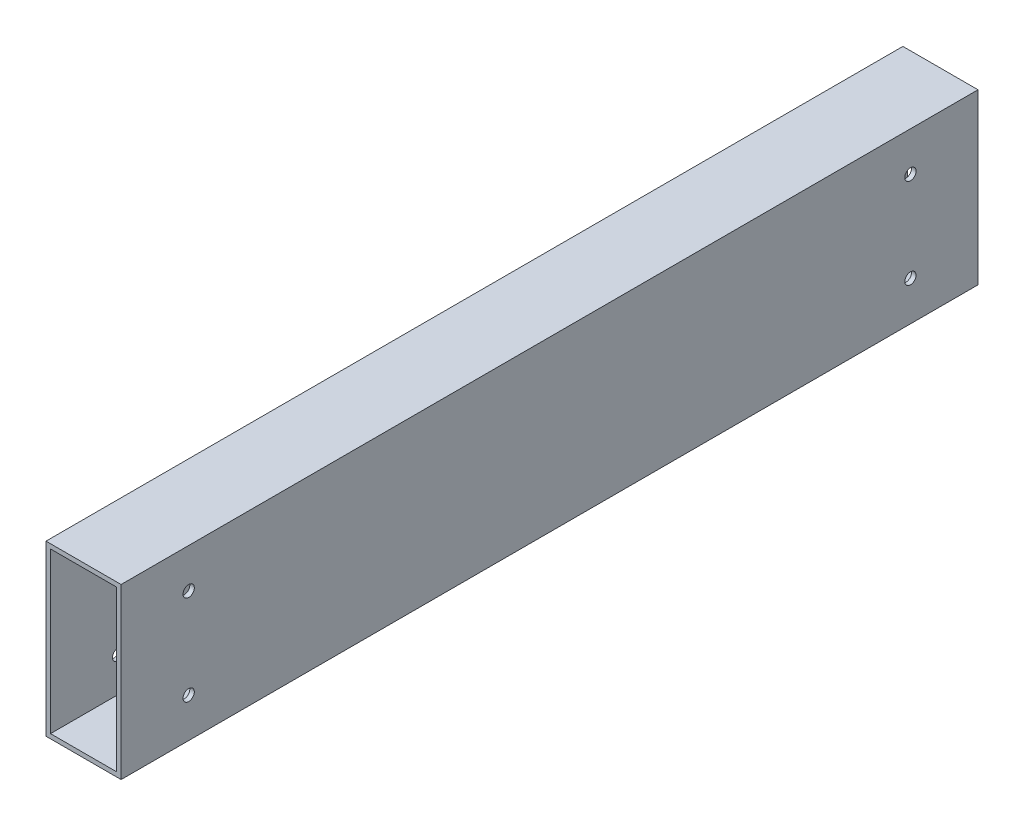
SolidWorks part; units mm, degrees
ref_plane "Alzado" through (0, 0, 0) normal (0, 0, 1) x (1, 0, 0)
ref_plane "Planta" through (0, 0, 0) normal (0, 1, 0) x (1, 0, 0)
ref_plane "Vista lateral" through (0, 0, 0) normal (1, 0, 0) x (0, 0, -1)
sketch "Croquis1" plane through (0, 0, 0) normal (0, 0, 1) x (1, 0, 0)
  line L1 (-10, -22.5) -> (10, -22.5)
  line L2 (-10, -22.5) -> (-10, 22.5)
  line L3 (-10, 22.5) -> (10, 22.5)
  line L4 (10, -22.5) -> (10, 22.5)
  line L5 (-10, -22.5) -> (10, 22.5) construction
  line L6 (-10, 22.5) -> (10, -22.5) construction
  point P0 (0, 0)
extrude "Saliente-Extruir1" add sketch "Croquis1" along normal blind 228.2
sketch "Croquis5" plane through (0, 0, 0) normal (0, 0, -1) x (-1, 0, 0)
  line L0 (-10, 22.5) -> (10, 22.5) construction
  line L1 (-8.8, 21.3) -> (8.8, 21.3)
  line L2 (-8.8, 21.3) -> (-8.8, -21.3)
  line L3 (-8.8, -21.3) -> (8.8, -21.3)
  line L4 (8.8, 21.3) -> (8.8, -21.3)
  line L5 (-8.8, 21.3) -> (8.8, -21.3) construction
  line L6 (-8.8, -21.3) -> (8.8, 21.3) construction
  line L7 (10, 22.5) -> (10, -22.5) construction
  point P0 (0, 0)
  dimension "D1" = 1.2
  dimension "D2" = 1.2
extrude "Cortar-Extruir3" cut sketch "Croquis5" against normal up to surface (228.2 mm away) up to face at (0, 0, 228.2)
sketch "Croquis6" plane through (10, 0, 0) normal (1, 0, 0) x (0, 0, -1)
  line L7 (-210.2, 12) -> (-18, -12) construction
  line L8 (-210.2, -12) -> (-18, 12) construction
  circle A0 centre (-210.2, -12) radius 1.5
  circle A1 centre (-210.2, 12) radius 1.5
  circle A2 centre (-18, 12) radius 1.5
  circle A3 centre (-18, -12) radius 1.5
  point P8 (-114.1, 0)
extrude "Cortar-Extruir4" cut sketch "Croquis6" against normal blind 30
